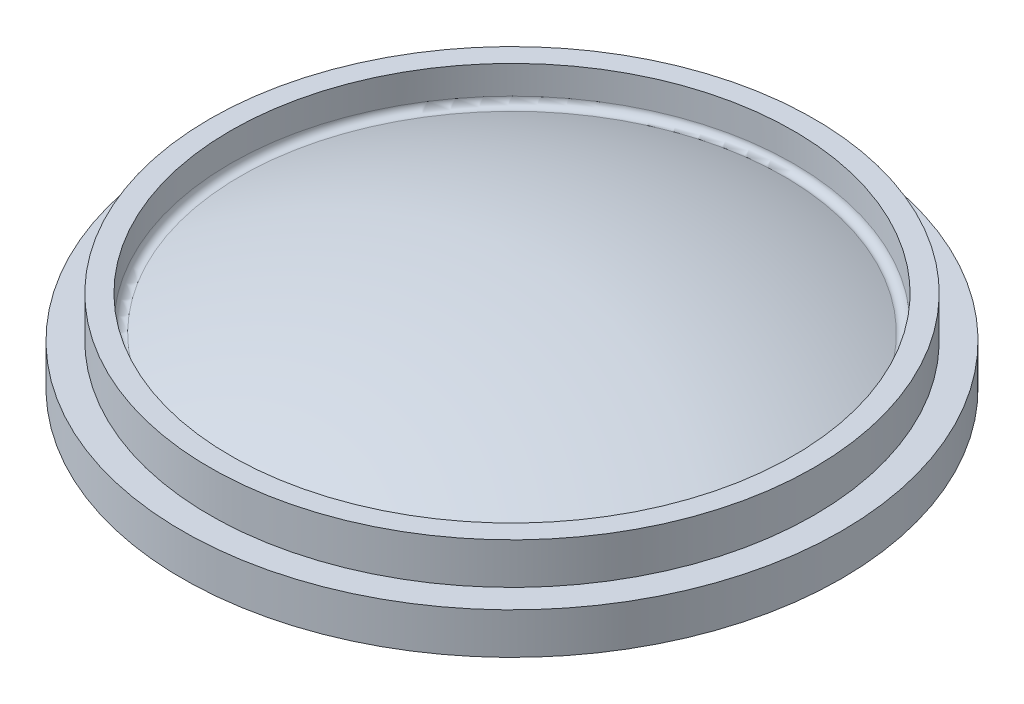
SolidWorks part; units mm, degrees
material "6061-T6 (SS)"
ref_plane "Front Plane" through (0, 0, 0) normal (0, 0, 1) x (1, 0, 0)
ref_plane "Top Plane" through (0, 0, 0) normal (0, 1, 0) x (1, 0, 0)
ref_plane "Right Plane" through (0, 0, 0) normal (1, 0, 0) x (0, 0, -1)
sketch "Sketch1" plane through (0, 0, 0) normal (0, 0, 1) x (1, 0, 0)
  line L0 (0, 49.2125) -> (0, 44.45)
  line L1 (152.4, 19.05) -> (152.4, 0)
  line L2 (152.4, 0) -> (147.6375, 0)
  line L3 (147.6375, 0) -> (147.6375, 4.3928)
  line L4 (152.4, 19.05) -> (139.7, 19.05)
  line L5 (139.7, 19.05) -> (139.7, 38.1)
  line L6 (139.7, 38.1) -> (130.175, 38.1)
  line L7 (130.175, 38.1) -> (130.175, 20.0164)
  arc A0 (130.175, 20.0164) -> (0, 49.2125) centre (0, -255.5875) ccw
  arc A1 (147.6375, 4.3928) -> (0, 44.45) centre (0, -247.65) ccw
  point P10 (150.0188, 0)
  dimension "D4" = 19.05
  dimension "D5" = 4.7625
  dimension "D1" = 304.8
  dimension "D7" = 9.525
  dimension "D9" = 292.1
  dimension "D10" = 19.05
  dimension "D2" = 152.4
  dimension "D3" = 25.4
  dimension "D6" = 12.7
  dimension "D8" = 4.7625
revolve "Revolve1" add sketch "Sketch1" angle 360 about L0
ref_plane "Plane1" through (0, 49.2125, 0) normal (0, 1, 0) x (1, 0, 0)
fillet "Fillet1" radius 3.175 1 edges at (-130.175, 20.0164, 0)
